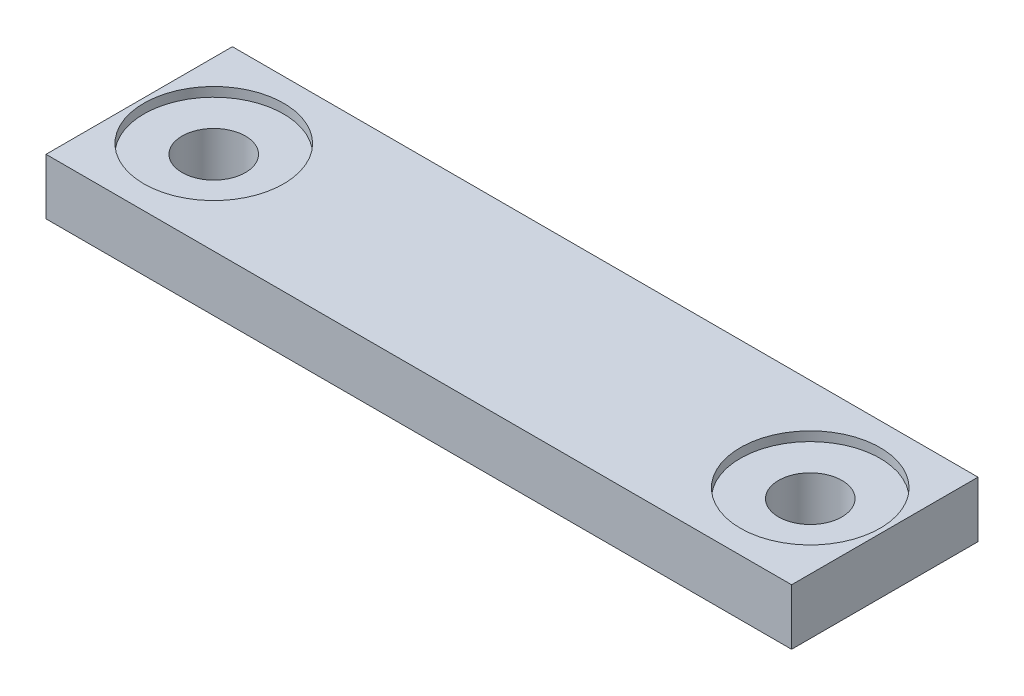
SolidWorks part; units mm, degrees
material "ABS"
ref_plane "Front Plane" through (0, 0, 0) normal (0, 0, 1) x (1, 0, 0)
ref_plane "Top Plane" through (0, 0, 0) normal (0, 1, 0) x (1, 0, 0)
ref_plane "Right Plane" through (0, 0, 0) normal (1, 0, 0) x (0, 0, -1)
sketch "Sketch1" plane through (0, 0, 0) normal (0, 1, 0) x (1, 0, 0)
  line L0 (0, -5) -> (4, -5) construction
  line L1 (0, 0) -> (40, 0)
  line L2 (0, 0) -> (0, -10)
  line L3 (0, -10) -> (40, -10)
  line L4 (40, 0) -> (40, -10)
  line L5 (40, -5) -> (36, -5) construction
  dimension "D1" = 40
  dimension "D2" = 10
  dimension "D3" = 4
extrude "Boss-Extrude1" add sketch "Sketch1" against normal blind 3
hole_wizard "CBORE for M3 Pan Head Machine Screw1" positions "Sketch4" profile "Sketch3" counterbore size "M3" standard "ANSI Metric" end condition up to next
sketch "Sketch4" plane through (0, 0, 0) normal (0, 1, 0) x (1, 0, 0)
  point P0 (4, -5)
  point P6 (36, -5)
sketch "Sketch3" plane through (4, 0, 5) normal (1, 0, 0) x (0, 0, 1)
  line L0 (0, 0) -> (0, 3)
  line L1 (0, 3) -> (1.7, 3)
  line L3 (1.7, 3) -> (1.7, 0.5)
  line L4 (1.7, 0.5) -> (3.75, 0.5)
  line L5 (3.75, 0.5) -> (3.75, 0)
  line L7 (3.75, 0) -> (0, 0)
  line L11 (0, -6.35) -> (0, 107.95) construction
  dimension "Thru Hole Dia." = 3.4
  dimension "Thru Hole Depth" = 3
  dimension "C'Bore Dia." = 7.5
  dimension "C'Bore Depth" = 0.5
equation "\"D1@Sketch1\"=8*2+24"
